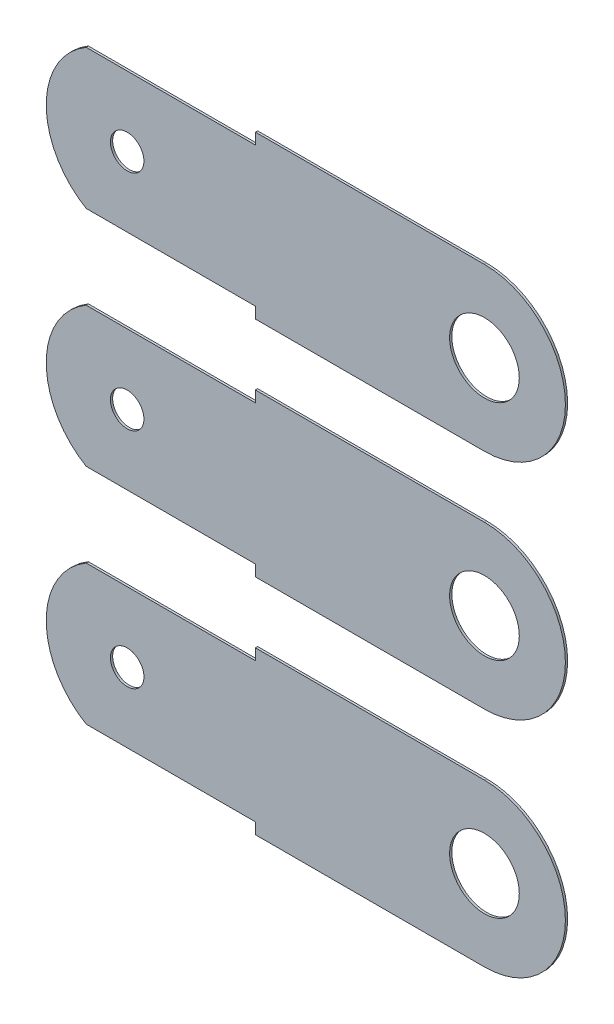
SolidWorks part; units mm, degrees
ref_plane "Front Plane" through (0, 0, 0) normal (0, 0, 1) x (1, 0, 0)
ref_plane "Top Plane" through (0, 0, 0) normal (0, 1, 0) x (1, 0, 0)
ref_plane "Right Plane" through (0, 0, 0) normal (1, 0, 0) x (0, 0, -1)
sketch "Sketch1" plane through (0, 0, 0) normal (0, 0, 1) x (1, 0, 0)
  line L0 (-9.906, 5.08) -> (-18.034, 5.08) construction
  line L2 (-9.906, 3.2385) -> (-18.034, 3.2385)
  line L3 (-9.906, 6.9215) -> (-18.034, 6.9215)
  arc A0 (-9.906, 3.2385) -> (-9.906, 6.9215) centre (-9.906, 5.08) ccw
  arc A1 (-18.034, 6.9215) -> (-18.034, 3.2385) centre (-18.034, 5.08) ccw
  circle A2 centre (-9.906, 5.08) radius 0.762 construction
  circle A3 centre (-18.034, 5.08) radius 0.381
  circle A4 centre (-9.906, 5.08) radius 0.7925 construction
  circle A5 centre (-9.906, 5.08) radius 0.7925
  point P5 (-13.97, 5.08)
  dimension "D2" = 8.128
  dimension "D3" = 0.762
  dimension "D1" = 3.683
extrude "Boss-Extrude1" add sketch "Sketch1" along normal blind 0.0508
sketch "Sketch2" plane through (0, 0, 0.0508) normal (0, 0, 1) x (1, 0, 0)
  line L0 (-15.1174, 7.3799) -> (-15.1174, 6.6675)
  line L1 (-15.1174, 6.6675) -> (-19.9247, 6.6675)
  line L2 (-15.1194, 3.4925) -> (-19.9247, 3.4925)
  line L3 (-15.1194, 3.4925) -> (-15.1194, 2.6963)
  line L4 (-15.1194, 2.6963) -> (-19.9247, 2.6963)
  line L5 (-19.9247, 2.6963) -> (-19.9247, 3.4925)
  line L6 (-19.9247, 6.6675) -> (-19.9247, 7.3799)
  line L7 (-19.9247, 7.3799) -> (-15.1174, 7.3799)
  line L8 (-18.034, 5.08) -> (-15.7061, 5.08) construction
  dimension "D1" = 3.175
extrude "Cut-Extrude1" cut sketch "Sketch2" against normal blind 0.0508
pattern_linear "LPattern1" count 3 spacing 5.08 along (0, -1, 0) of "Cut-Extrude1", "Boss-Extrude1"
